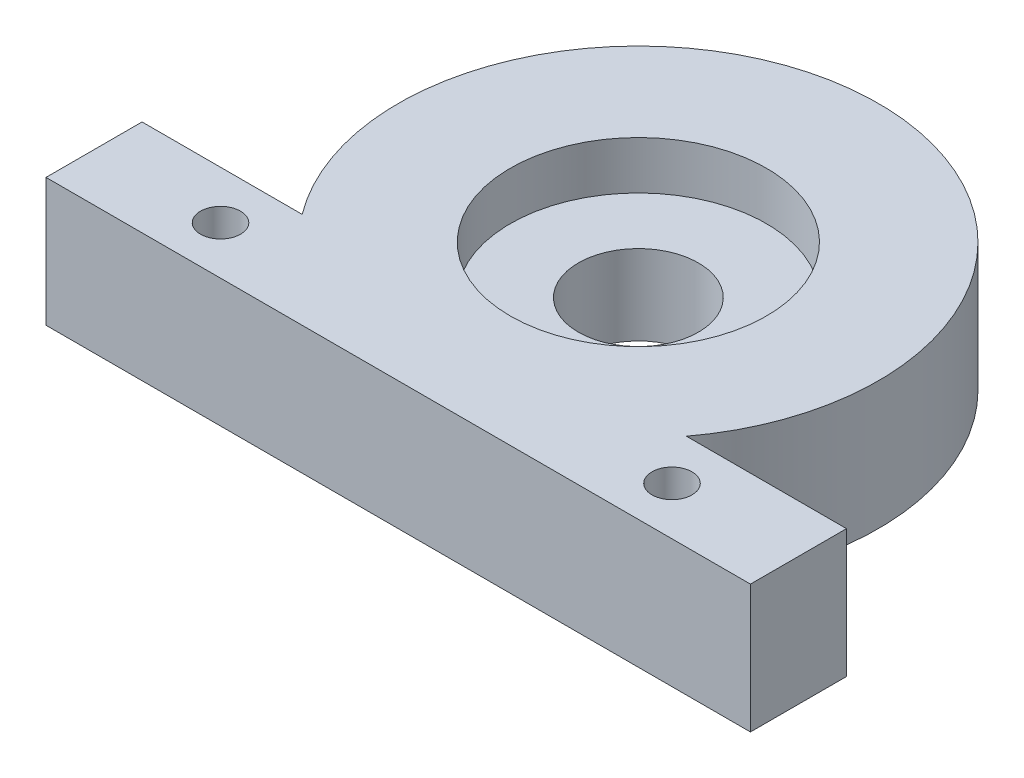
SolidWorks part; units mm, degrees
ref_plane "Front Plane" through (0, 0, 0) normal (0, 0, 1) x (1, 0, 0)
ref_plane "Top Plane" through (0, 0, 0) normal (0, 1, 0) x (1, 0, 0)
ref_plane "Right Plane" through (0, 0, 0) normal (1, 0, 0) x (0, 0, -1)
sketch "Sketch1" plane through (0, 0, 0) normal (0, 1, 0) x (1, 0, 0)
  line L0 (-6, -4.5) -> (-11, -4.5)
  line L1 (11, -7.5) -> (-11, -7.5)
  line L2 (11, -7.5) -> (11, -4.5)
  line L3 (11, -4.5) -> (6, -4.5)
  line L4 (-11, -7.5) -> (-11, -4.5)
  line L5 (11, -7.5) -> (-11, -4.5) construction
  line L6 (11, -4.5) -> (-11, -7.5) construction
  arc A0 (6, -4.5) -> (-6, -4.5) centre (0, 0) ccw
  circle A1 centre (-7.05, -6) radius 0.625
  circle A2 centre (7.05, -6) radius 0.625
  circle A3 centre (0, 0) radius 1.875
  point P3 (0, -6)
  dimension "D1" = 15
  dimension "D4" = 1.25
  dimension "D5" = 7.05
  dimension "D7" = 3.75
  dimension "D2" = 22
  dimension "D3" = 3
  dimension "D6" = 7.05
extrude "Boss-Extrude1" add sketch "Sketch1" along normal blind 4
sketch "Sketch2" plane through (0, 4, 0) normal (0, 1, 0) x (1, 0, 0)
  circle A0 centre (0, 0) radius 4
  dimension "D1" = 8
extrude "Cut-Extrude1" cut sketch "Sketch2" against normal blind 1.5
